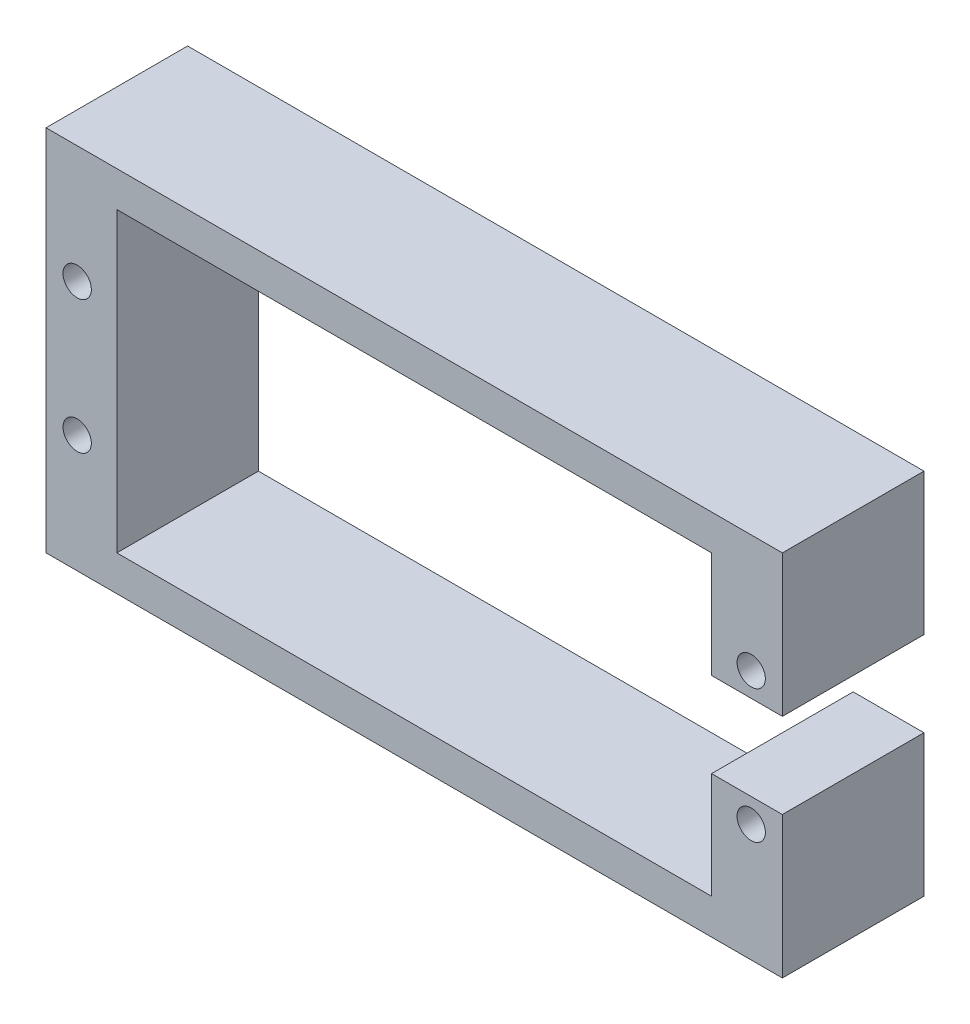
SolidWorks part; units mm, degrees
ref_plane "前基準面" through (0, 0, 0) normal (0, 0, 1) x (1, 0, 0)
ref_plane "上基準面" through (0, 0, 0) normal (0, 1, 0) x (1, 0, 0)
ref_plane "右基準面" through (0, 0, 0) normal (1, 0, 0) x (0, 0, -1)
sketch "草圖1" plane through (0, 0, 0) normal (0, 0, 1) x (1, 0, 0)
  line L0 (0, -55) -> (0, 55) construction
  line L1 (-21, 10.5) -> (21, 10.5)
  line L2 (-21, 10.5) -> (-21, -10.5)
  line L3 (-21, -10.5) -> (21, -10.5)
  line L4 (21, 10.5) -> (21, 3)
  line L5 (55, 0) -> (-55, 0) construction
  line L6 (26, -3) -> (26, -13)
  line L7 (-26, 13) -> (26, 13)
  line L8 (-26, 13) -> (-26, -13)
  line L9 (-26, -13) -> (26, -13)
  line L10 (26, 13) -> (26, 3)
  line L11 (21, 3) -> (26, 3)
  line L13 (21, -3) -> (26, -3)
  line L14 (21, -3) -> (21, -10.5)
  circle A0 centre (-23.8, 4.7) radius 1
  circle A2 centre (23.8, 4.7) radius 1
  circle A3 centre (23.8, -4.7) radius 1
  circle A4 centre (-23.8, -4.7) radius 1
  dimension "D10" = 2.8
  dimension "D1" = 42
  dimension "D2" = 21
  dimension "D3" = 21
  dimension "D4" = 10.5
  dimension "D5" = 52
  dimension "D6" = 26
  dimension "D7" = 26
  dimension "D8" = 13
  dimension "D9" = 5.8
  dimension "D11" = 6
  dimension "D12" = 3
extrude "填料-伸長1" add sketch "草圖1" along normal blind 10
